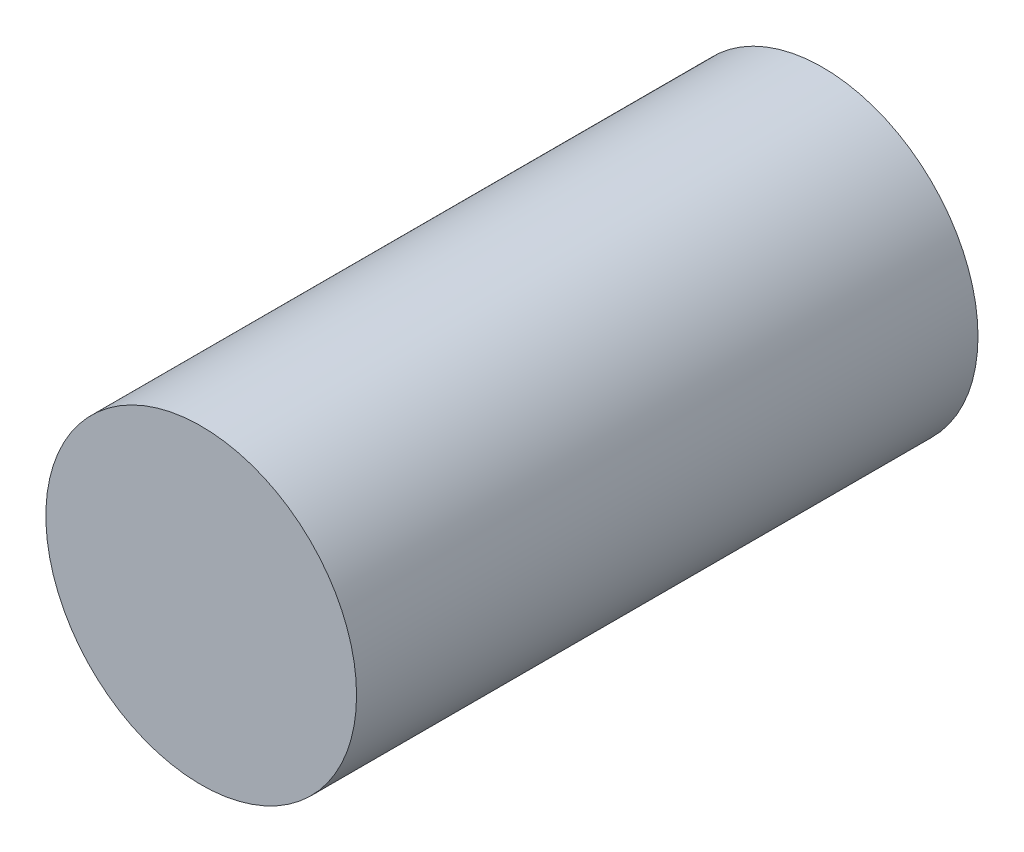
SolidWorks part; units mm, degrees
material "7075-T6 (SN)"
ref_plane "Front Plane" through (0, 0, 0) normal (0, 0, 1) x (1, 0, 0)
ref_plane "Top Plane" through (0, 0, 0) normal (0, 1, 0) x (1, 0, 0)
ref_plane "Right Plane" through (0, 0, 0) normal (1, 0, 0) x (0, 0, -1)
sketch "Sketch1" plane through (0, 0, 0) normal (0, 0, 1) x (1, 0, 0)
  circle A0 centre (0, 0) radius 25.4
  dimension "D1" = 50.8
extrude "Boss-Extrude1" add sketch "Sketch1" along normal blind 101.6
